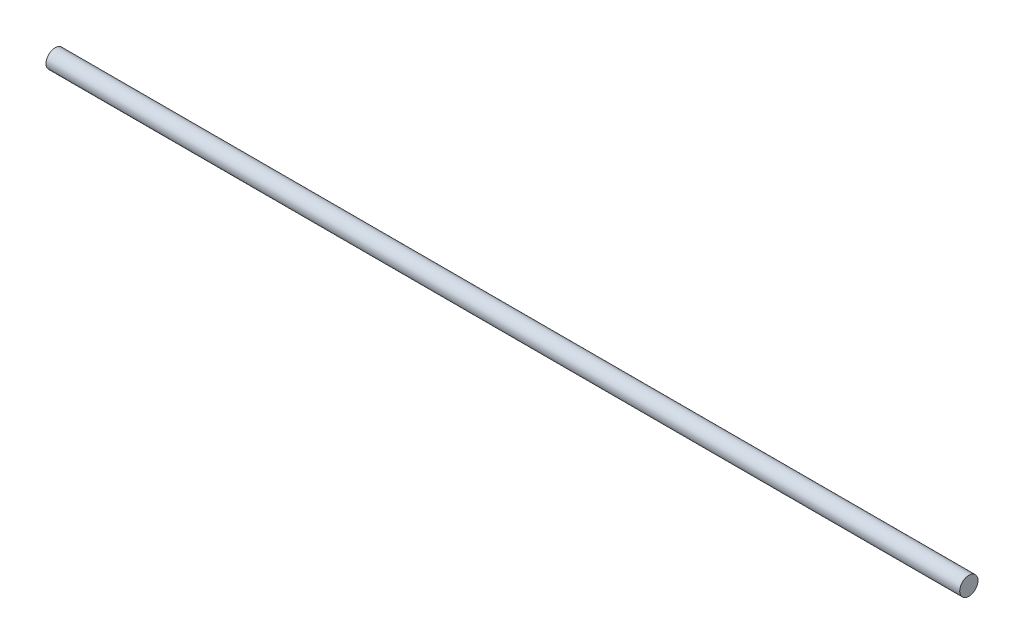
SolidWorks part; units mm, degrees
ref_plane "Front Plane" through (0, 0, 0) normal (0, 0, 1) x (1, 0, 0)
ref_plane "Top Plane" through (0, 0, 0) normal (0, 1, 0) x (1, 0, 0)
ref_plane "Right Plane" through (0, 0, 0) normal (1, 0, 0) x (0, 0, -1)
sketch "Sketch2" plane through (0, 0, 0) normal (1, 0, 0) x (0, 0, -1)
  circle A0 centre (0, 0) radius 4
  dimension "D1" = 8
extrude "Boss-Extrude1" add sketch "Sketch2" along normal blind 400
